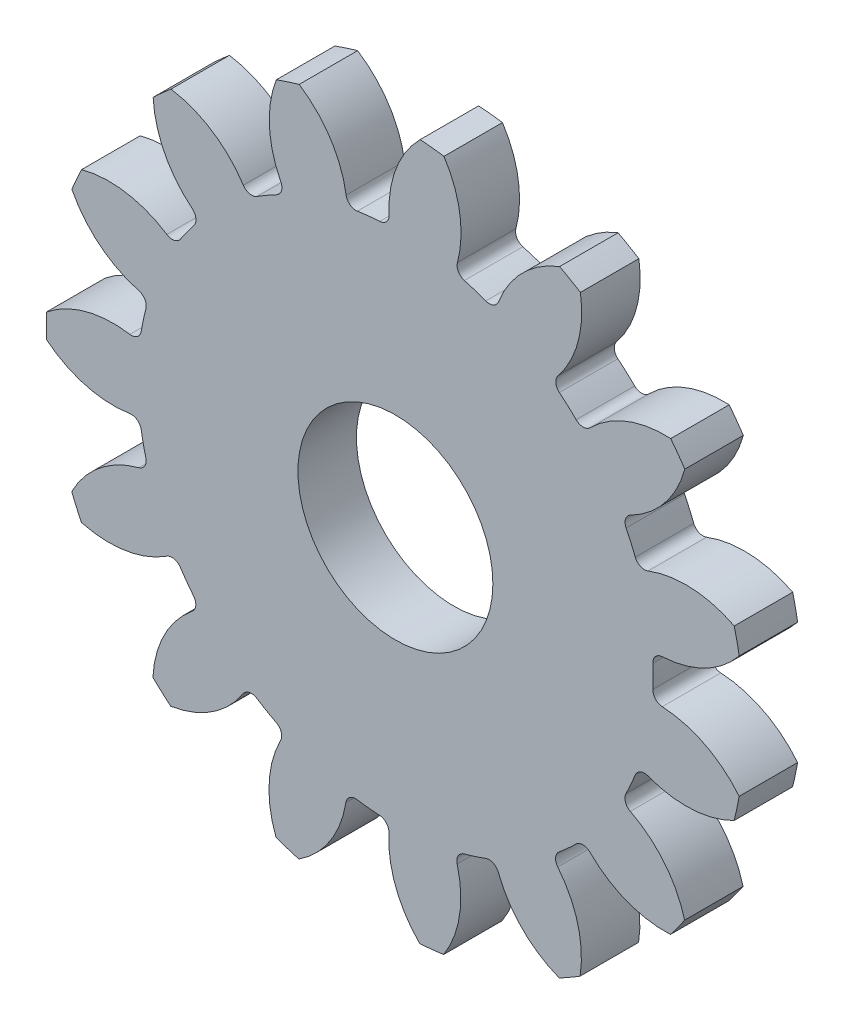
SolidWorks part; units mm, degrees
ref_plane "Alzado" through (0, 0, 0) normal (0, 0, 1) x (1, 0, 0)
ref_plane "Planta" through (0, 0, 0) normal (0, 1, 0) x (1, 0, 0)
ref_plane "Vista lateral" through (0, 0, 0) normal (1, 0, 0) x (0, 0, -1)
sketch "Croquis1" plane through (0, 0, 0) normal (0, 0, 1) x (1, 0, 0)
  circle A0 centre (0, 0) radius 17.907
  dimension "D1" = 35.814
extrude "Saliente-Extruir1" add sketch "Croquis1" along normal blind 3
sketch "Croquis2" plane through (0, 0, 3) normal (0, 0, 1) x (1, 0, 0)
  line L0 (0, 0) -> (0, 15.875) construction
  line L1 (0, 0) -> (7.2227, 19.8441) construction
  line L2 (0, 0) -> (-1.651, 15.7889) construction
  line L3 (0, 15.875) -> (5.1021, 14.018) construction
  arc A0 (1.2677, 17.8621) -> (-4.9354, 17.2134) centre (0, 0) ccw
  arc A2 (-0.2682, 13.218) -> (-2.472, 12.9875) centre (0, 0) ccw
  arc A3 (1.2677, 17.8621) -> (-0.2682, 13.218) centre (5.1021, 14.018) ccw
  arc A4 (-4.9354, 17.2134) -> (-2.472, 12.9875) centre (-7.8917, 12.6593) cw
  dimension "D2" = 26.4414
  dimension "D3" = 20
  dimension "D4" = 1.651
extrude "Cortar-Extruir1" cut sketch "Croquis2" against normal through all
fillet "Redondeo1" radius 0.508 2 edges at (-0.2682, 13.218, 1.5) (-2.472, 12.9875, 1.5)
pattern_circular "MatrizC1" count 15 over 360 about axis through (0, 0, 0) along (0, 0, 1) of "Redondeo1", "Cortar-Extruir1"
sketch "Croquis3" plane through (0, 0, 3) normal (0, 0, 1) x (1, 0, 0)
  circle A0 centre (0, 0) radius 5
  dimension "D1" = 10
extrude "Cortar-Extruir2" cut sketch "Croquis3" against normal through all
